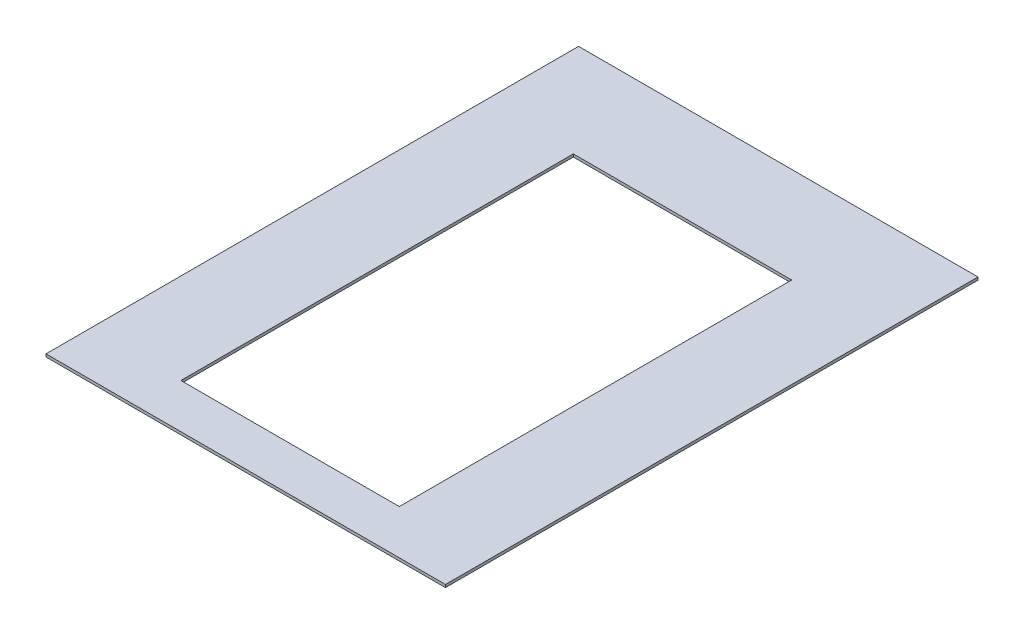
SolidWorks part; units mm, degrees
ref_plane "Front Plane" through (0, 0, 0) normal (0, 0, 1) x (1, 0, 0)
ref_plane "Top Plane" through (0, 0, 0) normal (0, 1, 0) x (1, 0, 0)
ref_plane "Right Plane" through (0, 0, 0) normal (1, 0, 0) x (0, 0, -1)
sketch "Sketch1" plane through (0, 0, 0) normal (0, 1, 0) x (1, 0, 0)
  line L0 (0, 0) -> (0, 195.2) construction
  line L1 (-228.6, -304.8) -> (228.6, -304.8)
  line L2 (-228.6, -304.8) -> (-228.6, 304.8)
  line L3 (-228.6, 304.8) -> (228.6, 304.8)
  line L4 (228.6, -304.8) -> (228.6, 304.8)
  line L5 (-228.6, -304.8) -> (228.6, 304.8) construction
  line L6 (-228.6, 304.8) -> (228.6, -304.8) construction
  line L7 (-125, 195.2) -> (125, 195.2)
  line L8 (-125, 195.2) -> (-125, -254)
  line L9 (-125, -254) -> (125, -254)
  line L10 (125, 195.2) -> (125, -254)
  point P0 (0, 0)
  dimension "D1" = 609.6
  dimension "D2" = 250
  dimension "D3" = 449.2
  dimension "D4" = 50.8
  dimension "D5" = 457.2
extrude "Boss-Extrude1" add sketch "Sketch1" along normal mid plane 3.175
